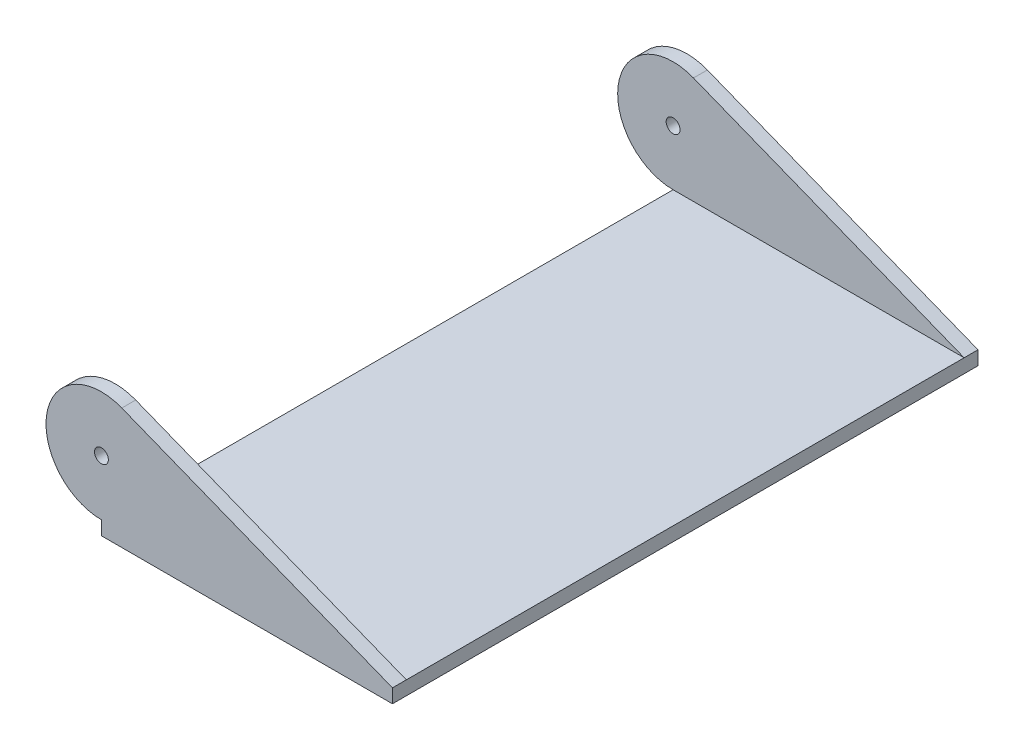
SolidWorks part; units mm, degrees
ref_plane "Front Plane" through (0, 0, 0) normal (0, 0, 1) x (1, 0, 0)
ref_plane "Top Plane" through (0, 0, 0) normal (0, 1, 0) x (1, 0, 0)
ref_plane "Right Plane" through (0, 0, 0) normal (1, 0, 0) x (0, 0, -1)
sketch "Sketch2" plane through (0, 0, 0) normal (0, 1, 0) x (1, 0, 0)
  line L1 (-25.2326, 84.3337) -> (8.1049, 84.3337)
  line L2 (-25.2326, 84.3337) -> (-25.2326, 17.2619)
  line L3 (-25.2326, 17.2619) -> (8.1049, 17.2619)
  line L4 (8.1049, 84.3337) -> (8.1049, 17.2619)
  dimension "D1" = 67.0719
  dimension "D2" = 33.3375
extrude "Boss-Extrude1" add sketch "Sketch2" along normal blind 1.5875 contours L2 L3 L4 L1
sketch "Sketch3" plane through (0, 0, -17.2619) normal (0, 0, 1) x (1, 0, 0)
  line L0 (-25.2326, 1.5875) -> (-25.2326, 7.9375) construction
  line L1 (8.1049, 1.5875) -> (-22.8983, 13.8429)
  line L2 (-25.2326, 1.5875) -> (8.1049, 1.5875)
  circle A0 centre (-25.2326, 7.9375) radius 6.35
  circle A1 centre (-25.2326, 7.9375) radius 0.7937
  dimension "D1" = 6.35
  dimension "D2" = 1.5875
extrude "Boss-Extrude2" add sketch "Sketch3" against normal up to surface (67.0719 mm away)
sketch "Sketch4" plane through (8.1049, 0, 0) normal (1, 0, 0) x (0, 0, -1)
  line L0 (84.3337, 1.5875) -> (17.2619, 1.5875) construction
  line L1 (18.8494, 1.5875) -> (82.7462, 1.5875)
  line L2 (18.8494, 1.5875) -> (18.8494, 14.2875)
  line L3 (18.8494, 14.2875) -> (82.7462, 14.2875)
  line L4 (82.7462, 1.5875) -> (82.7462, 14.2875)
  line L5 (84.3337, 14.2875) -> (17.2619, 14.2875) construction
  line L6 (17.2619, 1.5875) -> (17.2619, 13.8429) construction
  line L7 (84.3337, 1.5875) -> (84.3337, 13.8429) construction
  dimension "D1" = 1.5875
  dimension "D2" = 1.5875
extrude "Cut-Extrude1" cut sketch "Sketch4" against normal through all
